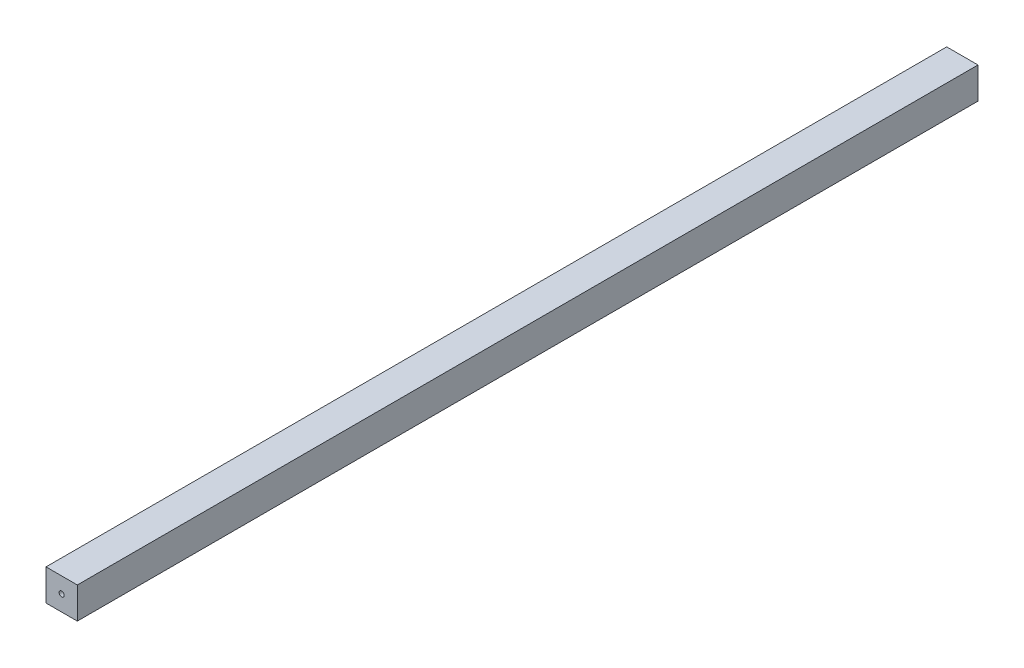
SolidWorks part; units mm, degrees
ref_plane "Front Plane" through (0, 0, 0) normal (0, 0, 1) x (1, 0, 0)
ref_plane "Top Plane" through (0, 0, 0) normal (0, 1, 0) x (1, 0, 0)
ref_plane "Right Plane" through (0, 0, 0) normal (1, 0, 0) x (0, 0, -1)
sketch "Sketch1" plane through (0, 0, 0) normal (0, 0, 1) x (1, 0, 0)
  line L1 (-12.7, -12.7) -> (12.7, -12.7)
  line L2 (-12.7, -12.7) -> (-12.7, 12.7)
  line L3 (-12.7, 12.7) -> (12.7, 12.7)
  line L4 (12.7, -12.7) -> (12.7, 12.7)
  line L5 (-12.7, -12.7) -> (12.7, 12.7) construction
  line L6 (-12.7, 12.7) -> (12.7, -12.7) construction
  point P0 (0, 0)
  dimension "D1" = 25.4
  dimension "D2" = 25.4
extrude "Boss-Extrude1" add sketch "Sketch1" along normal mid plane 730.25
sketch "Sketch2" plane through (0, 0, 365.125) normal (0, 0, 1) x (1, 0, 0)
  circle A0 centre (0, 0) radius 2.0828
  dimension "D1" = 4.1656
extrude "Cut-Extrude1" cut sketch "Sketch2" against normal blind 812.292
